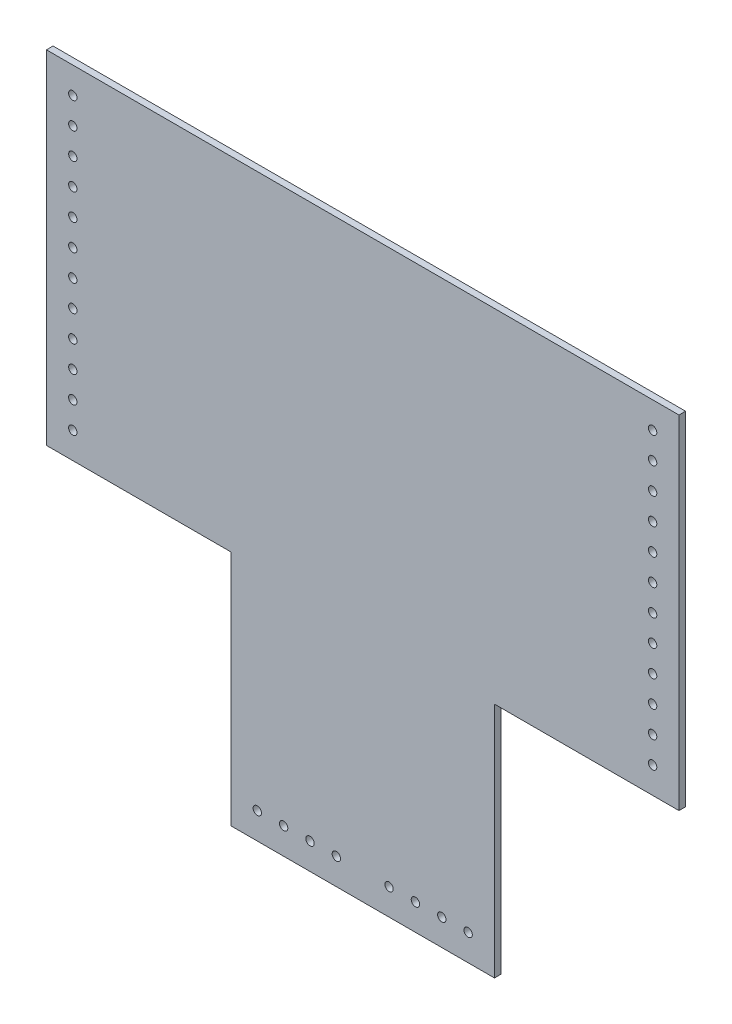
SolidWorks part; units mm, degrees
material "PC High Viscosity"
ref_plane "Front Plane" through (0, 0, 0) normal (0, 0, 1) x (1, 0, 0)
ref_plane "Top Plane" through (0, 0, 0) normal (0, 1, 0) x (1, 0, 0)
ref_plane "Right Plane" through (0, 0, 0) normal (1, 0, 0) x (0, 0, -1)
sketch "Sketch1" plane through (0, 0, 0) normal (0, 0, 1) x (1, 0, 0)
  line L0 (0, 114.3) -> (88.9, 114.3)
  line L1 (88.9, 0) -> (215.9, 0)
  line L2 (0, 114.3) -> (0, 279.4)
  line L3 (0, 279.4) -> (304.8, 279.4)
  line L4 (304.8, 0) -> (304.8, 279.4) construction
  line L5 (88.9, 114.3) -> (88.9, 0)
  line L6 (152.4, 0) -> (152.4, 279.4) construction
  line L7 (0, 0) -> (0, 114.3) construction
  line L8 (0, 0) -> (88.9, 0) construction
  line L9 (152.4, 279.4) -> (304.8, 279.4) construction
  line L10 (152.4, 0) -> (304.8, 0) construction
  line L11 (101.6, 12.7) -> (114.3, 12.7) construction
  line L12 (12.7, 127) -> (12.7, 139.7) construction
  line L13 (292.1, 127) -> (292.1, 139.7) construction
  line L14 (203.2, 12.7) -> (190.5, 12.7) construction
  line L15 (304.8, 0) -> (215.9, 0) construction
  line L16 (304.8, 0) -> (304.8, 114.3) construction
  line L17 (215.9, 114.3) -> (215.9, 0)
  line L18 (304.8, 114.3) -> (304.8, 279.4)
  line L19 (304.8, 114.3) -> (215.9, 114.3)
  circle A0 centre (101.6, 12.7) radius 2.0193
  circle A1 centre (114.3, 12.7) radius 2.0193
  circle A2 centre (127, 12.7) radius 2.0193
  circle A3 centre (139.7, 12.7) radius 2.0193
  circle A4 centre (12.7, 127) radius 2.0193
  circle A5 centre (12.7, 139.7) radius 2.0193
  circle A6 centre (12.7, 152.4) radius 2.0193
  circle A7 centre (12.7, 165.1) radius 2.0193
  circle A8 centre (12.7, 177.8) radius 2.0193
  circle A9 centre (12.7, 190.5) radius 2.0193
  circle A10 centre (12.7, 203.2) radius 2.0193
  circle A11 centre (12.7, 215.9) radius 2.0193
  circle A12 centre (12.7, 228.6) radius 2.0193
  circle A13 centre (12.7, 241.3) radius 2.0193
  circle A14 centre (12.7, 254) radius 2.0193
  circle A15 centre (12.7, 266.7) radius 2.0193
  circle A16 centre (292.1, 266.7) radius 2.0193
  circle A17 centre (292.1, 254) radius 2.0193
  circle A18 centre (292.1, 241.3) radius 2.0193
  circle A19 centre (292.1, 228.6) radius 2.0193
  circle A20 centre (292.1, 215.9) radius 2.0193
  circle A21 centre (292.1, 203.2) radius 2.0193
  circle A22 centre (292.1, 190.5) radius 2.0193
  circle A23 centre (292.1, 177.8) radius 2.0193
  circle A24 centre (292.1, 165.1) radius 2.0193
  circle A25 centre (292.1, 152.4) radius 2.0193
  circle A26 centre (292.1, 139.7) radius 2.0193
  circle A27 centre (292.1, 127) radius 2.0193
  circle A28 centre (165.1, 12.7) radius 2.0193
  circle A29 centre (177.8, 12.7) radius 2.0193
  circle A30 centre (190.5, 12.7) radius 2.0193
  circle A31 centre (203.2, 12.7) radius 2.0193
  dimension "D5" = 12.7
  dimension "D6" = 12.7
  dimension "D7" = 4.0386
  dimension "D10" = 12.7
  dimension "D11" = 12.7
  dimension "D12" = 4.0386
  dimension "D1" = 279.4
  dimension "D2" = 304.8
  dimension "D3" = 114.3
  dimension "D4" = 88.9
  dimension "D9" = 12.7
  dimension "D14" = 12.7
  dimension "D8" = 4
  dimension "D13" = 12
extrude "Boss-Extrude1" add sketch "Sketch1" along normal blind 3.175
